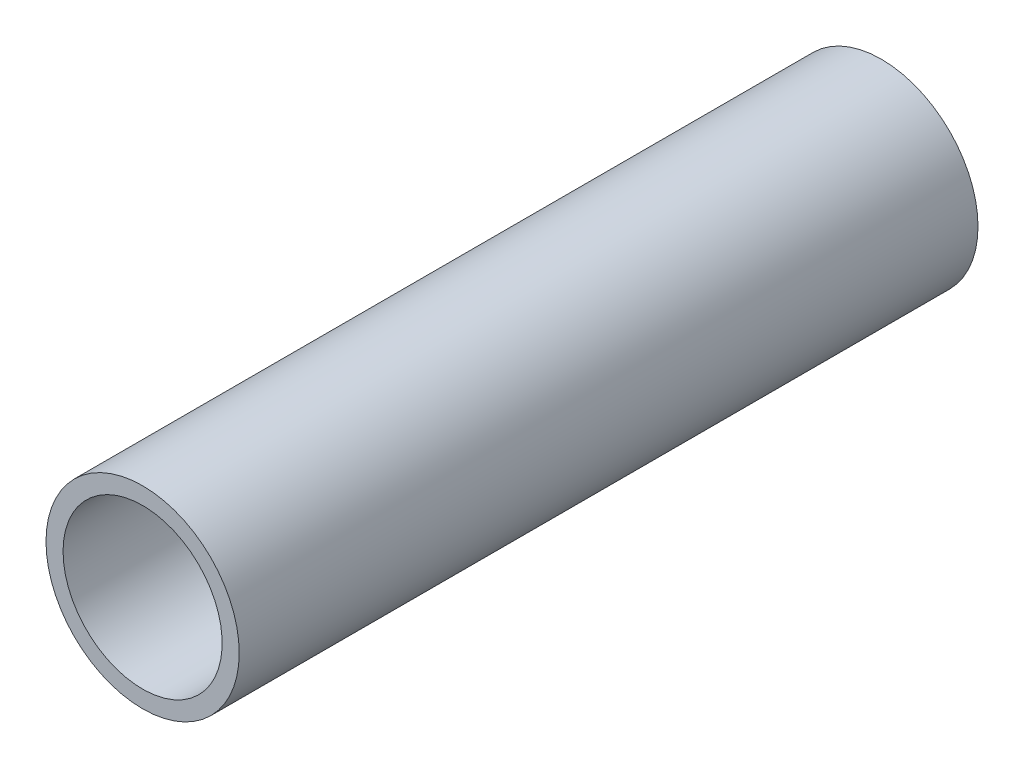
SolidWorks part; units mm, degrees
material "Plain Carbon Steel"
ref_plane "Front Plane" through (0, 0, 0) normal (0, 0, 1) x (1, 0, 0)
ref_plane "Top Plane" through (0, 0, 0) normal (0, 1, 0) x (1, 0, 0)
ref_plane "Right Plane" through (0, 0, 0) normal (1, 0, 0) x (0, 0, -1)
sketch "Sketch1" plane through (0, 0, 0) normal (0, 0, 1) x (1, 0, 0)
  circle A0 centre (347.5, -26) radius 17
  circle A1 centre (347.5, -26) radius 14
  arc A4 (364.5, -26) -> (330.5, -26) centre (347.5, -26) ccw construction
  dimension "D1" = 28
extrude "Boss-Extrude1" add sketch "Sketch1" along normal offset from surface 20 and the other way offset from surface (90 mm away) 10
